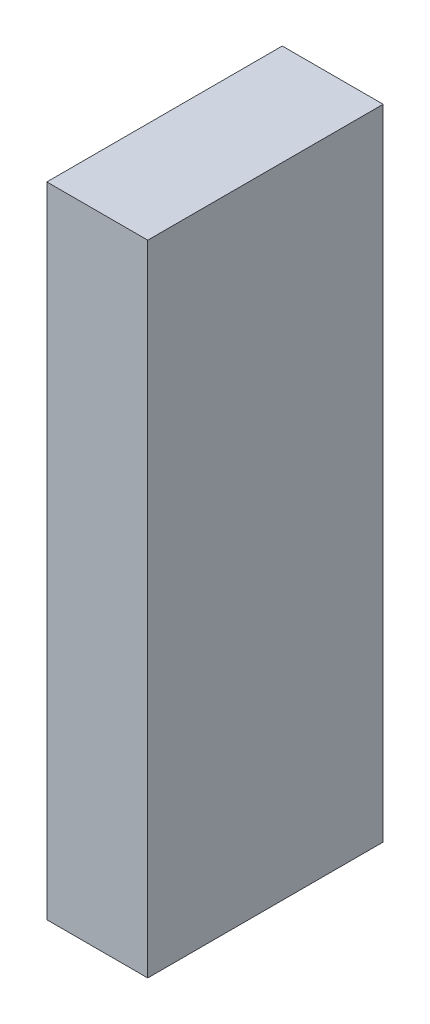
SolidWorks part; units mm, degrees
ref_plane "Front Plane" through (0, 0, 0) normal (0, 0, 1) x (1, 0, 0)
ref_plane "Top Plane" through (0, 0, 0) normal (0, 1, 0) x (1, 0, 0)
ref_plane "Right Plane" through (0, 0, 0) normal (1, 0, 0) x (0, 0, -1)
sketch "Sketch1" plane through (0, 0, 0) normal (0, 1, 0) x (1, 0, 0)
  line L1 (19.05, -44.45) -> (-19.05, -44.45)
  line L2 (19.05, -44.45) -> (19.05, 44.45)
  line L3 (19.05, 44.45) -> (-19.05, 44.45)
  line L4 (-19.05, -44.45) -> (-19.05, 44.45)
  line L5 (19.05, -44.45) -> (-19.05, 44.45) construction
  line L6 (19.05, 44.45) -> (-19.05, -44.45) construction
  point P0 (0, 0)
  dimension "D1" = 38.1
  dimension "D2" = 88.9
extrude "Boss-Extrude1" add sketch "Sketch1" along normal mid plane 241.3
